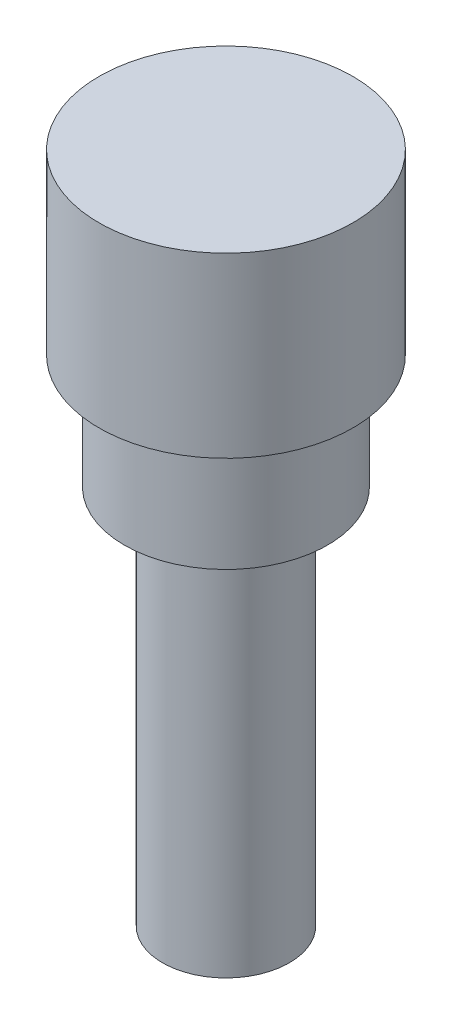
SolidWorks part; units mm, degrees
material "Stainless Steel (ferritic)"
ref_plane "Front Plane" through (0, 0, 0) normal (0, 0, 1) x (1, 0, 0)
ref_plane "Top Plane" through (0, 0, 0) normal (0, 1, 0) x (1, 0, 0)
ref_plane "Right Plane" through (0, 0, 0) normal (1, 0, 0) x (0, 0, -1)
sketch "Sketch2" plane through (0, 0, 0) normal (0, 0, 1) x (1, 0, 0)
  line L0 (0, 0) -> (-5, 0)
  line L1 (-5, 0) -> (-5, -7)
  line L2 (-5, -7) -> (-4, -7)
  line L3 (-4, -7) -> (-4, -11.5)
  line L4 (-4, -11.5) -> (-2.5, -11.5)
  line L5 (-2.5, -11.5) -> (-2.5, -26.5)
  line L6 (-2.5, -26.5) -> (0, -26.5)
  line L7 (0, -26.5) -> (0, 0)
  point P3 (0, -28.2804)
  dimension "D1" = 2.5
  dimension "D2" = 5
  dimension "D3" = 4
  dimension "D4" = 15
  dimension "D5" = 4.5
  dimension "D6" = 7
revolve "Revolve1" add sketch "Sketch2" angle 360 about L7
cosmetic thread "Cosmetic Thread1" parameters "D2"=4.11
